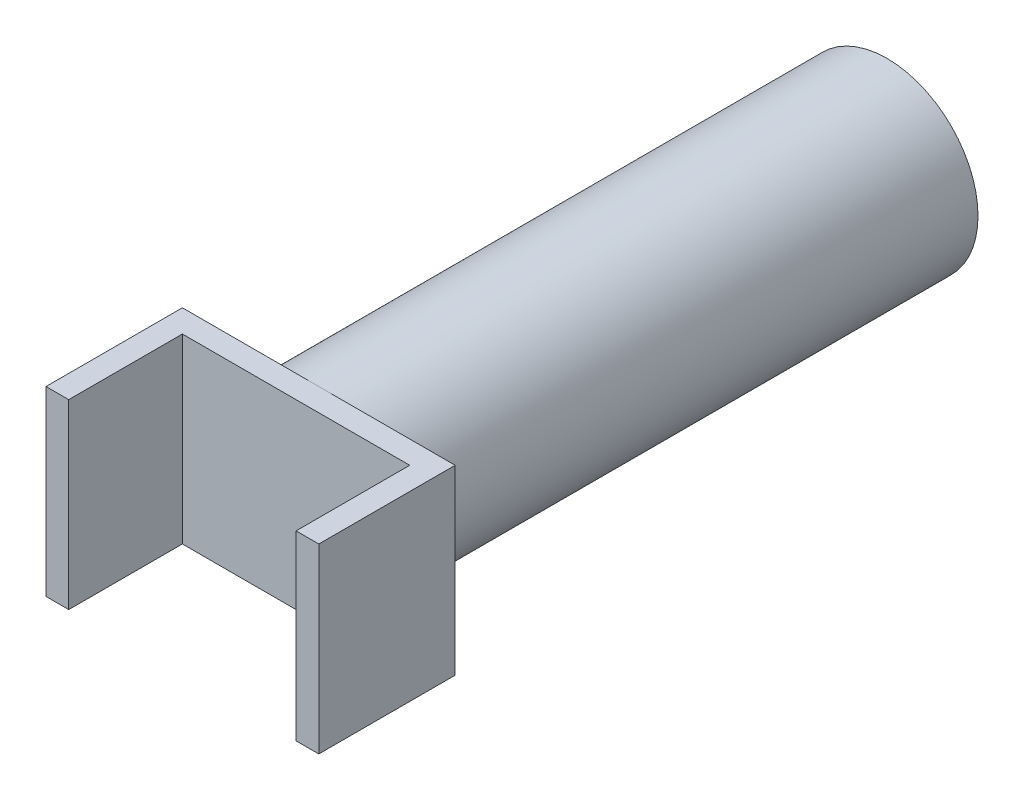
SolidWorks part; units mm, degrees
ref_plane "Płaszczyzna przednia" through (0, 0, 0) normal (0, 0, 1) x (1, 0, 0)
ref_plane "Płaszczyzna górna" through (0, 0, 0) normal (0, 1, 0) x (1, 0, 0)
ref_plane "Płaszczyzna prawa" through (0, 0, 0) normal (1, 0, 0) x (0, 0, -1)
sketch "Szkic1" plane through (0, 0, 0) normal (0, 0, 1) x (1, 0, 0)
  circle A0 centre (0, 0) radius 40
  dimension "D1" = 80
extrude "Dodanie-wyciągnięcie1" add sketch "Szkic1" along normal blind 250
sketch "Szkic2" plane through (0, 0, 250) normal (0, 0, 1) x (1, 0, 0)
  line L1 (60, 40) -> (-60, 40)
  line L2 (60, 40) -> (60, -40)
  line L3 (60, -40) -> (-60, -40)
  line L4 (-60, 40) -> (-60, -40)
  line L5 (60, 40) -> (-60, -40) construction
  line L6 (60, -40) -> (-60, 40) construction
  point P0 (0, 0)
  dimension "D1" = 120
  dimension "D2" = 80
extrude "Dodanie-wyciągnięcie2" add sketch "Szkic2" along normal blind 10
sketch "Szkic3" plane through (0, 0, 260) normal (0, 0, 1) x (1, 0, 0)
  line L0 (0, 0) -> (0, -52.2355) construction
  line L1 (0, -52.2355) -> (0, 50.2644) construction
  line L2 (-60, -40) -> (60, -40) construction
  line L3 (-60, 40) -> (-50, 40)
  line L4 (-60, 40) -> (-60, -40)
  line L5 (-60, -40) -> (-50, -40)
  line L6 (-50, 40) -> (-50, -40)
  line L7 (50, 40) -> (50, -40)
  line L8 (60, -40) -> (50, -40)
  line L9 (60, 40) -> (60, -40)
  line L10 (60, 40) -> (50, 40)
  dimension "D1" = 10
extrude "Dodanie-wyciągnięcie3" add sketch "Szkic3" along normal blind 50
sketch "Szkic4" plane through (0, 0, 260) normal (0, 0, 1) x (1, 0, 0)
  point P0 (0, 0)
